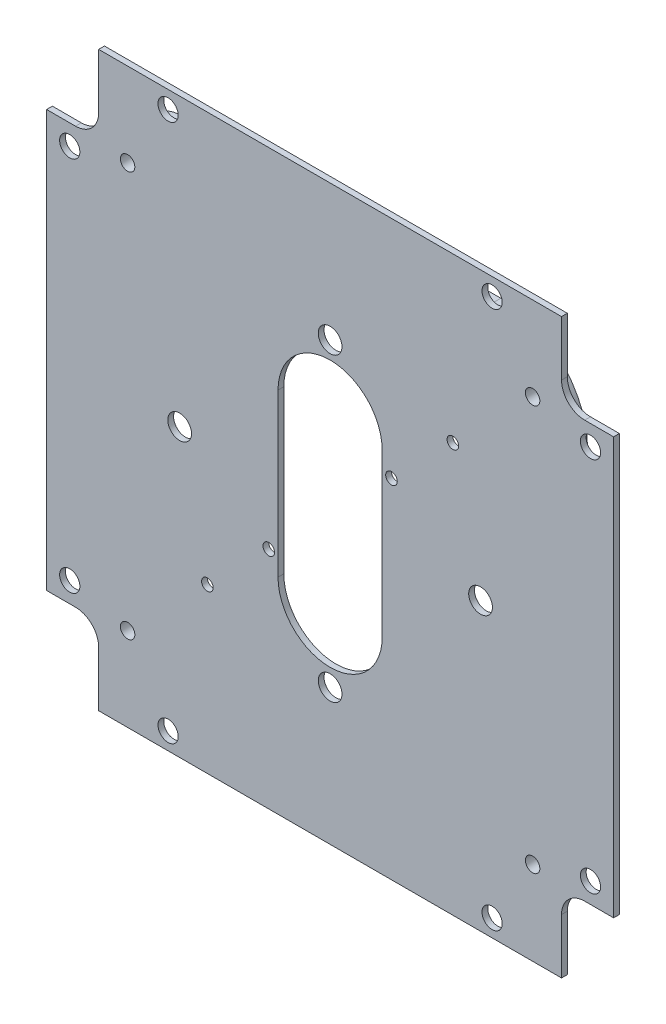
SolidWorks part; units mm, degrees
material "6061-T6 (SS)"
ref_plane "Front Plane" through (0, 0, 0) normal (0, 0, 1) x (1, 0, 0)
ref_plane "Top Plane" through (0, 0, 0) normal (0, 1, 0) x (1, 0, 0)
ref_plane "Right Plane" through (0, 0, 0) normal (1, 0, 0) x (0, 0, -1)
sketch "Sketch1" plane through (0, 0, 0) normal (0, 0, 1) x (1, 0, 0)
  line L1 (0, 0) -> (98, 0)
  line L2 (0, 0) -> (0, 99)
  line L3 (0, 99) -> (98, 99)
  line L4 (98, 0) -> (98, 99)
  dimension "D1" = 98
  dimension "D2" = 99
extrude "Main Body" add sketch "Sketch1" along normal blind 1
sketch "Sketch2" plane through (0, 0, 1) normal (0, 0, 1) x (1, 0, 0)
  line L0 (49, 82) -> (49, 99) construction
  line L1 (4, 82) -> (94, 82) construction
  line L2 (4, 82) -> (4, 17) construction
  line L3 (4, 17) -> (94, 17) construction
  line L4 (94, 82) -> (94, 17) construction
  line L5 (98, 99) -> (0, 99) construction
  line L6 (0, 99) -> (0, 0) construction
  line L7 (94, 49.5) -> (98, 49.5) construction
  line L8 (98, 0) -> (98, 99) construction
  circle A0 centre (4, 82) radius 1.75
  circle A1 centre (94, 82) radius 1.75
  circle A2 centre (94, 17) radius 1.75
  circle A3 centre (4, 17) radius 1.75
  dimension "D3" = 3.5
  dimension "D1" = 4
  dimension "D2" = 65
extrude "FrontBackBoltHoles" cut sketch "Sketch2" against normal through all
sketch "Sketch3" plane through (0, 0, 1) normal (0, 0, 1) x (1, 0, 0)
  line L0 (49, 96) -> (49, 99) construction
  line L1 (21, 96) -> (77, 96) construction
  line L2 (21, 96) -> (21, 3) construction
  line L3 (21, 3) -> (77, 3) construction
  line L4 (77, 96) -> (77, 3) construction
  line L5 (98, 99) -> (0, 99) construction
  line L7 (77, 49.5) -> (98, 49.5) construction
  line L8 (98, 0) -> (98, 99) construction
  circle A0 centre (21, 96) radius 1.75
  circle A1 centre (77, 96) radius 1.75
  circle A2 centre (77, 3) radius 1.75
  circle A3 centre (21, 3) radius 1.75
  dimension "D3" = 3.5
  dimension "D1" = 56
  dimension "D2" = 93
extrude "SideBoltHoles" cut sketch "Sketch3" against normal through all
sketch "Sketch4" plane through (0, 0, 1) normal (0, 0, 1) x (1, 0, 0)
  line L0 (12.5, 49.5) -> (85.5, 49.5) construction
  line L1 (12.5, 94.5) -> (85.5, 94.5) construction
  line L2 (12.5, 94.5) -> (12.5, 4.5) construction
  line L3 (12.5, 4.5) -> (85.5, 4.5) construction
  line L4 (85.5, 94.5) -> (85.5, 4.5) construction
  line L5 (49, 49.5) -> (49, 94.5) construction
  line L6 (12.5, 49.5) -> (0, 49.5) construction
  line L7 (0, 99) -> (0, 0) construction
  line L8 (49, 94.5) -> (49, 99) construction
  line L9 (85.5, 49.5) -> (98, 49.5) construction
  line L10 (98, 0) -> (98, 99) construction
  line L11 (98, 99) -> (0, 99) construction
  line L13 (49, 4.5) -> (49, 0) construction
  line L14 (0, 0) -> (98, 0) construction
  point P8 (35, 49.5)
  point P22 (63, 49.5)
  dimension "D1" = 90
  dimension "D2" = 73
  dimension "D3" = 14
  dimension "D4" = 14
sketch "Sketch7" plane through (0, 0, 1) normal (0, 0, 1) x (1, 0, 0)
  line L0 (0, 49.5) -> (9, 49.5) construction
  line L1 (9, 85.5) -> (89, 85.5) construction
  line L2 (9, 85.5) -> (9, 13.5) construction
  line L3 (9, 13.5) -> (89, 13.5) construction
  line L4 (89, 85.5) -> (89, 13.5) construction
  line L5 (0, 99) -> (0, 0) construction
  line L7 (49, 85.5) -> (49, 99) construction
  line L8 (98, 99) -> (0, 99) construction
  line L9 (9, 85.5) -> (0, 85.5)
  line L10 (9, 85.5) -> (9, 99)
  line L11 (9, 99) -> (0, 99)
  line L12 (0, 85.5) -> (0, 99)
  line L13 (89, 85.5) -> (98, 85.5)
  line L14 (89, 85.5) -> (89, 99)
  line L15 (89, 99) -> (98, 99)
  line L16 (98, 85.5) -> (98, 99)
  line L17 (98, 0) -> (89, 0)
  line L18 (98, 0) -> (98, 13.5)
  line L19 (98, 13.5) -> (89, 13.5)
  line L20 (89, 0) -> (89, 13.5)
  line L21 (0, 0) -> (9, 0)
  line L22 (0, 0) -> (0, 13.5)
  line L23 (0, 13.5) -> (9, 13.5)
  line L24 (9, 0) -> (9, 13.5)
  dimension "D1" = 80
  dimension "D2" = 72
extrude "Cut-Extrude3" cut sketch "Sketch7" against normal through all
fillet "Fillet1" radius 4 4 edges at (89, 85.5, 0.5) (9, 13.5, 0.5) (89, 13.5, 0.5) (9, 85.5, 0.5)
sketch "Sketch8" plane through (0, 0, 0) normal (0, 0, -1) x (-1, 0, 0)
  line L0 (-79, 90.5) -> (-79, 8.5) construction
  line L1 (-79, 90.5) -> (-19, 90.5)
  line L2 (-79, 90.5) -> (-79, 93.5)
  line L3 (-79, 93.5) -> (-19, 93.5)
  line L4 (-19, 90.5) -> (-19, 93.5)
  line L5 (-79, 8.5) -> (-13.7737, 8.5)
  line L6 (-79, 8.5) -> (-79, 5.5)
  line L7 (-79, 5.5) -> (-13.7737, 5.5)
  line L8 (-13.7737, 8.5) -> (-13.7737, 5.5)
  line L9 (-79, 49.5) -> (-98, 49.5) construction
  line L10 (-98, 13.5) -> (-98, 85.5) construction
  line L11 (-49, 93.5) -> (-49, 99) construction
  line L12 (-89, 99) -> (-9, 99) construction
  dimension "D1" = 3
  dimension "D2" = 3
  dimension "D3" = 88
  dimension "D4" = 60
extrude "Boss-Extrude2" [suppressed] add sketch "Sketch8" along normal blind 2
sketch "Sketch9" plane through (0, 0, 0) normal (0, 0, -1) x (-1, 0, 0)
  line L0 (-87.5, 79.5) -> (-10.5, 79.5) construction
  line L1 (-90.5, 79.5) -> (-87.5, 79.5)
  line L2 (-90.5, 79.5) -> (-90.5, 19.5)
  line L3 (-90.5, 19.5) -> (-87.5, 19.5)
  line L4 (-87.5, 79.5) -> (-87.5, 19.5)
  line L5 (-10.5, 79.5) -> (-7.5, 79.5)
  line L6 (-10.5, 79.5) -> (-10.5, 23.6787)
  line L7 (-10.5, 23.6787) -> (-7.5, 23.6787)
  line L8 (-7.5, 79.5) -> (-7.5, 23.6787)
  line L9 (-49, 79.5) -> (-49, 99) construction
  line L10 (-89, 99) -> (-9, 99) construction
  line L12 (-90.5, 49.5) -> (-98, 49.5) construction
  line L13 (-98, 13.5) -> (-98, 85.5) construction
  dimension "D1" = 83
  dimension "D2" = 3
  dimension "D3" = 3
  dimension "D4" = 60
extrude "Boss-Extrude3" [suppressed] add sketch "Sketch9" along normal blind 2
sketch "Sketch15" plane through (0, 0, 0) normal (0, 0, -1) x (-1, 0, 0)
  line L0 (-49, 49.5) -> (-98, 49.5) construction
  line L1 (-22.5, 93.5) -> (-75.5, 93.5)
  line L2 (-7.5, 78.5) -> (-7.5, 20.5)
  line L3 (-22.5, 5.5) -> (-75.5, 5.5)
  line L4 (-90.5, 78.5) -> (-90.5, 20.5)
  line L5 (-7.5, 93.5) -> (-90.5, 5.5) construction
  line L6 (-7.5, 5.5) -> (-90.5, 93.5) construction
  line L7 (-98, 13.5) -> (-98, 85.5) construction
  line L9 (-9, 0) -> (-89, 0) construction
  line L10 (-49, 0) -> (-49, 49.5) construction
  line L11 (-35.5, 90.5) -> (-62.5, 90.5)
  line L12 (-10.5, 65.5) -> (-10.5, 33.5)
  line L13 (-35.5, 8.5) -> (-62.5, 8.5)
  line L14 (-87.5, 65.5) -> (-87.5, 33.5)
  line L15 (-10.5, 90.5) -> (-87.5, 8.5) construction
  line L16 (-10.5, 8.5) -> (-87.5, 90.5) construction
  arc A0 (-10.5, 33.5) -> (-35.5, 8.5) centre (-35.5, 33.5) cw
  arc A1 (-35.5, 90.5) -> (-10.5, 65.5) centre (-35.5, 65.5) cw
  arc A2 (-62.5, 90.5) -> (-87.5, 65.5) centre (-62.5, 65.5) ccw
  arc A3 (-62.5, 8.5) -> (-87.5, 33.5) centre (-62.5, 33.5) cw
  arc A4 (-7.5, 20.5) -> (-22.5, 5.5) centre (-22.5, 20.5) cw
  arc A5 (-22.5, 93.5) -> (-7.5, 78.5) centre (-22.5, 78.5) cw
  arc A6 (-75.5, 93.5) -> (-90.5, 78.5) centre (-75.5, 78.5) ccw
  arc A7 (-75.5, 5.5) -> (-90.5, 20.5) centre (-75.5, 20.5) cw
  point P0 (-49, 49.5)
  dimension "D5" = 25
  dimension "D6" = 15
  dimension "D1" = 83
  dimension "D2" = 88
  dimension "D3" = 3
  dimension "D4" = 3
extrude "Boss-Extrude4" add sketch "Sketch15" along normal blind 2
sketch "Sketch10" plane through (0, 0, 1) normal (0, 0, 1) x (1, 0, 0)
  line L0 (0, 49.5) -> (49, 49.5) construction
  line L1 (0, 85.5) -> (0, 13.5) construction
  line L2 (49, 49.5) -> (49, 0) construction
  line L3 (9, 0) -> (89, 0) construction
  line L4 (49, 35.5) -> (49, 63.5) construction
  line L5 (40, 35.5) -> (40, 63.5)
  line L6 (58, 35.5) -> (58, 63.5)
  arc A1 (40, 35.5) -> (58, 35.5) centre (49, 35.5) ccw
  arc A2 (58, 63.5) -> (40, 63.5) centre (49, 63.5) ccw
  point P9 (49, 49.5)
  dimension "D1" = 9
  dimension "D2" = 28
extrude "CameraViewHole" cut sketch "Sketch10" against normal through all
sketch "Sketch11" plane through (0, 0, 1) normal (0, 0, 1) x (1, 0, 0)
  line L0 (49, 49.5) -> (0, 49.5) construction
  line L1 (84, 84.5) -> (14, 84.5) construction
  line L2 (84, 84.5) -> (84, 14.5) construction
  line L3 (84, 14.5) -> (14, 14.5) construction
  line L4 (14, 84.5) -> (14, 14.5) construction
  line L5 (84, 84.5) -> (14, 14.5) construction
  line L6 (84, 14.5) -> (14, 84.5) construction
  line L7 (0, 85.5) -> (0, 13.5) construction
  line L9 (9, 0) -> (89, 0) construction
  line L10 (49, 0) -> (49, 49.5) construction
  point P0 (49, 49.5)
  dimension "D1" = 70
hole_wizard "M3x0.5 Tapped Hole1" positions "Sketch12" profile "Sketch13" tap size "M3x0.5" standard "ANSI Metric"
sketch "Sketch12" plane through (0, 0, 1) normal (0, 0, 1) x (1, 0, 0)
  point P0 (84, 14.5)
  point P3 (14, 14.5)
  point P6 (14, 84.5)
  point P9 (84, 84.5)
sketch "Sketch13" plane through (84, 14.5, 1) normal (1, 0, 0) x (0, -1, 0)
  line L0 (0, 0) -> (0, 8.2511)
  line L1 (0, 8.2511) -> (1.25, 7.5)
  line L2 (1.25, 7.5) -> (1.25, 0)
  line L5 (1.25, 0) -> (0, 0)
  line L10 (0, 8.2511) -> (-1.25, 7.5) construction
  line L11 (0, -6.35) -> (0, 107.95) construction
  dimension "Tap Drill Dia." = 2.5
  dimension "Tap Drill Depth" = 7.5
  dimension "Drill Angle" = 118
sketch "Sketch16" plane through (0, 0, 1) normal (0, 0, 1) x (1, 0, 0)
  line L0 (14, 14.5) -> (70.213, 14.5) construction
  line L1 (70.213, 14.5) -> (70.213, 70.713) construction
  line L2 (59.607, 14.5) -> (59.607, 60.107) construction
  line L4 (38.393, 14.5) -> (38.393, 38.893) construction
  line L6 (27.787, 14.5) -> (27.787, 28.287) construction
  circle A0 centre (27.787, 28.287) radius 1
  circle A1 centre (38.393, 38.893) radius 1
  circle A2 centre (59.607, 60.107) radius 1
  circle A3 centre (70.213, 70.713) radius 1
  dimension "D9" = 2
  dimension "D1" = 13.787
  dimension "D2" = 13.787
  dimension "D3" = 24.393
  dimension "D4" = 24.393
  dimension "D5" = 45.607
  dimension "D6" = 45.607
  dimension "D7" = 56.213
  dimension "D8" = 56.213
extrude "WirePassthroughs" cut sketch "Sketch16" against normal through all
sketch "Sketch17" plane through (0, 0, 1) normal (0, 0, 1) x (1, 0, 0)
  line L0 (84, 23.5) -> (49, 23.5) construction
  line L1 (14, 84.5) -> (14, 49.5) construction
  line L2 (14, 49.5) -> (23, 49.5) construction
  line L3 (84, 14.5) -> (84, 49.5) construction
  line L4 (84, 49.5) -> (75, 49.5) construction
  line L6 (14, 84.5) -> (49, 84.5) construction
  line L7 (49, 84.5) -> (49, 75.5) construction
  circle A0 centre (49, 23.5) radius 2.05
  circle A1 centre (23, 49.5) radius 2.05
  circle A2 centre (49, 75.5) radius 2.05
  circle A3 centre (75, 49.5) radius 2.05
  dimension "D9" = 4.1
  dimension "D1" = 35
  dimension "D2" = 9
  dimension "D3" = 35
  dimension "D4" = 9
  dimension "D5" = 9
  dimension "D6" = 9
  dimension "D7" = 35
  dimension "D8" = 35
extrude "NotSureIfNeedPassthrough" cut sketch "Sketch17" against normal through all
